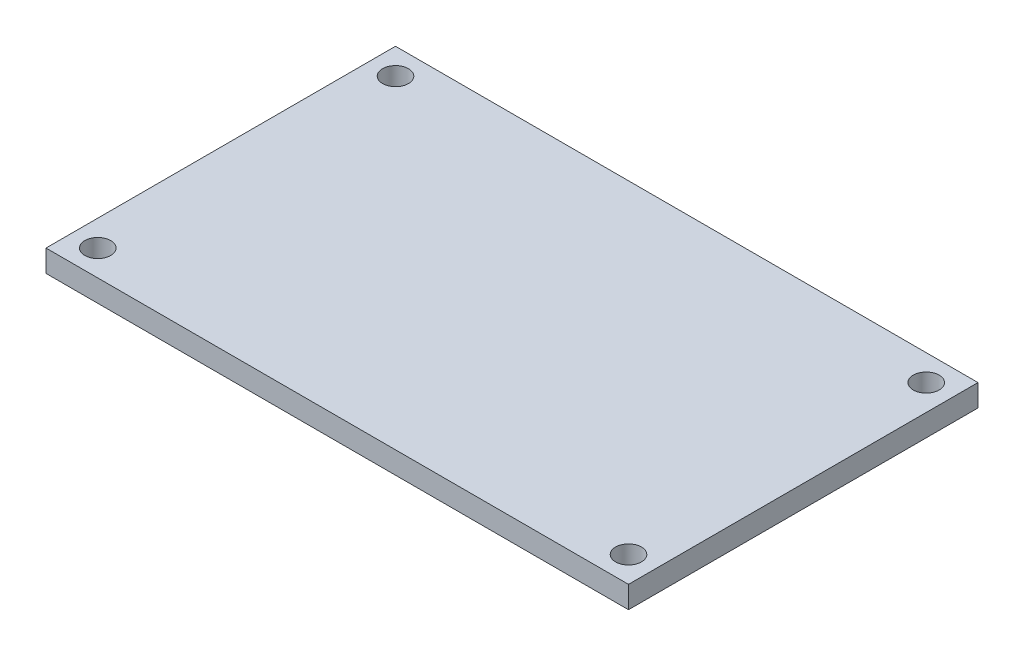
SolidWorks part; units mm, degrees
ref_plane "Plano frontal" through (0, 0, 0) normal (0, 0, 1) x (1, 0, 0)
ref_plane "Plano superior" through (0, 0, 0) normal (0, 1, 0) x (1, 0, 0)
ref_plane "Plano direito" through (0, 0, 0) normal (1, 0, 0) x (0, 0, -1)
sketch "Esboço1" plane through (0, 0, 0) normal (0, 1, 0) x (1, 0, 0)
  line L1 (0, 0) -> (45, 0)
  line L2 (0, 0) -> (0, 27)
  line L3 (0, 27) -> (45, 27)
  line L4 (45, 0) -> (45, 27)
  dimension "D1" = 45
  dimension "D2" = 27
extrude "Ressalto-extrusão1" add sketch "Esboço1" along normal blind 1.7
sketch "Esboço2" plane through (0, 0, 0) normal (0, -1, 0) x (1, 0, 0)
  line L0 (45, 0) -> (0, -27) construction
  line L1 (45, -27) -> (0, 0) construction
  line L2 (3, -22.5) -> (5, -24.5)
  line L3 (5, -2.5) -> (40, -2.5)
  line L4 (3, -4.5) -> (3, -22.5)
  line L5 (5, -24.5) -> (40, -24.5)
  line L6 (42, -4.5) -> (42, -22.5)
  line L7 (3, -2.5) -> (42, -24.5) construction
  line L8 (3, -24.5) -> (42, -2.5) construction
  line L9 (5, -2.5) -> (3, -4.5)
  line L10 (40, -2.5) -> (42, -4.5)
  line L11 (40, -24.5) -> (42, -22.5)
  point P8 (22.5, -13.5)
  dimension "D1" = 22
  dimension "D2" = 39
extrude "Ressalto-extrusão2" add sketch "Esboço2" along normal blind 1
sketch "Esboço3" plane through (0, 0, 0) normal (0, -1, 0) x (1, 0, 0)
  line L0 (45, -27) -> (0, -27) construction
  line L1 (0, -27) -> (0, 0) construction
  line L2 (22.5, 0) -> (22.5, -27) construction
  line L3 (0, 0) -> (45, 0) construction
  line L4 (0, -13.5) -> (45, -13.5) construction
  line L5 (45, 0) -> (45, -27) construction
  circle A0 centre (2, -25) radius 1
  circle A1 centre (43, -25) radius 1
  circle A2 centre (43, -2) radius 1
  circle A3 centre (2, -2) radius 1
  dimension "D1" = 2
  dimension "D2" = 2
  dimension "D3" = 2
extrude "Corte-extrusão1" cut sketch "Esboço3" against normal through all
